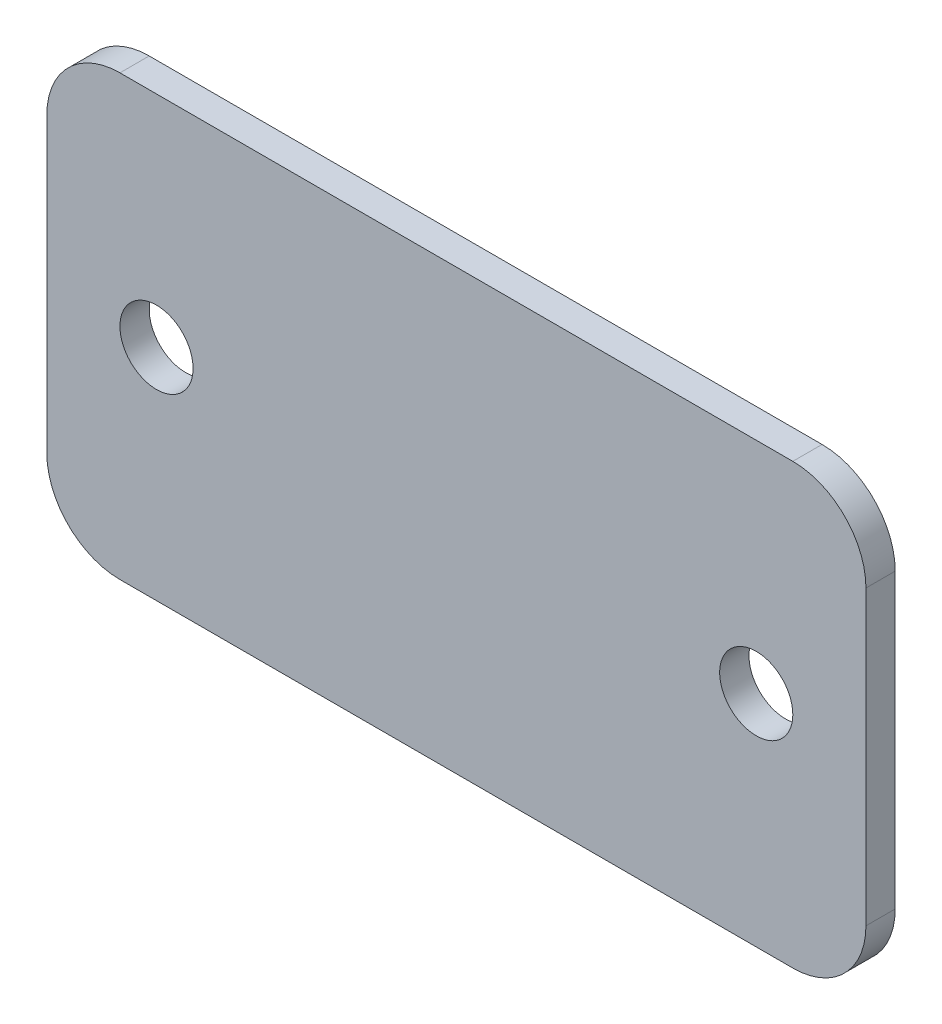
SolidWorks part; units mm, degrees
ref_plane "Plan de face" through (0, 0, 0) normal (0, 0, 1) x (1, 0, 0)
ref_plane "Plan de dessus" through (0, 0, 0) normal (0, 1, 0) x (1, 0, 0)
ref_plane "Plan de droite" through (0, 0, 0) normal (1, 0, 0) x (0, 0, -1)
sketch "Esquisse1" plane through (0, 0, 0) normal (0, 0, 1) x (1, 0, 0)
  line L1 (46, -30) -> (-46, -30)
  line L2 (56, -20) -> (56, 20)
  line L3 (46, 30) -> (-46, 30)
  line L4 (-56, -20) -> (-56, 20)
  line L5 (56, -30) -> (-56, 30) construction
  line L6 (56, 30) -> (-56, -30) construction
  line L9 (41, 0) -> (-41, 0) construction
  circle A0 centre (-41, 0) radius 5
  circle A1 centre (41, 0) radius 5
  arc A2 (-46, -30) -> (-56, -20) centre (-46, -20) cw
  arc A3 (46, -30) -> (56, -20) centre (46, -20) ccw
  arc A4 (56, 20) -> (46, 30) centre (46, 20) ccw
  arc A5 (-46, 30) -> (-56, 20) centre (-46, 20) ccw
  point P0 (0, 0)
extrude "Boss.-Extru.1" add sketch "Esquisse1" along normal blind 4
equation "\"D2@Esquisse1\"=30+82"
